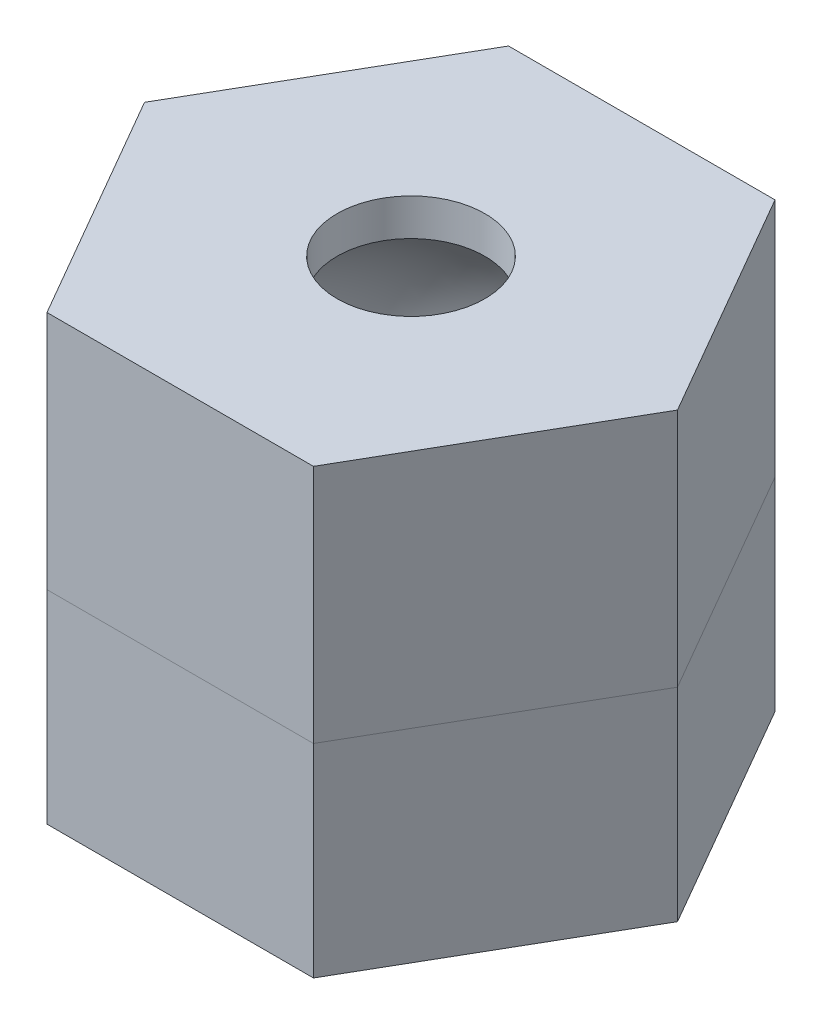
SolidWorks part; units mm, degrees
other "Downer"
other "Upper"
material "ABS"
ref_plane "Front Plane" through (0, 0, 0) normal (0, 0, 1) x (1, 0, 0)
ref_plane "Top Plane" through (0, 0, 0) normal (0, 1, 0) x (1, 0, 0)
ref_plane "Right Plane" through (0, 0, 0) normal (1, 0, 0) x (0, 0, -1)
sketch "Sketch2" plane through (0, 0, 0) normal (0, 1, 0) x (1, 0, 0)
  line L1 (72.1688, 0) -> (36.0844, 62.5)
  line L2 (36.0844, 62.5) -> (-36.0844, 62.5)
  line L3 (-36.0844, 62.5) -> (-72.1688, 0)
  line L4 (-72.1688, 0) -> (-36.0844, -62.5)
  line L5 (-36.0844, -62.5) -> (36.0844, -62.5)
  line L6 (36.0844, -62.5) -> (72.1688, 0)
  circle A0 centre (0, 0) radius 62.5 construction
  dimension "D1" = 125
extrude "Boss" add sketch "Sketch2" along normal blind 110
sketch "Sketch3" plane through (0, 0, 0) normal (1, 0, 0) x (0, 0, -1)
  line L0 (0, 110) -> (0, 7.5305)
  line L1 (0, 110) -> (0, 0) construction
  line L2 (0, 110) -> (20, 110)
  line L3 (0, 7.5305) -> (20, 7.5305)
  arc A0 (20, 7.5305) -> (20, 110) centre (0, 58.7652) ccw
  dimension "D2" = 110
  dimension "D1" = 20
revolve "Void" cut sketch "Sketch3" angle 360 about L0
ref_plane "Split Plane" through (0, 55, 0) normal (0, 1, 0) x (1, 0, 0)
split "Split" trim tools "Split Plane" bodies to split 102 resulting bodies 104 105
sketch "Sketch6" plane through (0, 55, 0) normal (0, 1, 0) x (1, 0, 0)
  circle A0 centre (62.5, 0) radius 5
  circle A1 centre (31.25, -54.1266) radius 5
  circle A2 centre (-31.25, -54.1266) radius 5
  circle A3 centre (-62.5, 0) radius 5
  circle A4 centre (-31.25, 54.1266) radius 5
  circle A5 centre (31.25, 54.1266) radius 5
  point P2 (34.8698, -68.7666)
  point P3 (0, 0)
  point P4 (-29.077, -55.3243)
  point P16 (0, 0)
  point P17 (0, 0)
  dimension "D2" = 10
  dimension "D1" = 62.5
  dimension "D3" = 6
extrude "Tab Holes" cut sketch "Sketch6" along direction (0, 1, 0) on the side of the normal blind 11
sketch "Sketch7" plane through (0, 55, 0) normal (0, 1, 0) x (1, 0, 0)
  circle A6 centre (62.5, 0) radius 5 construction
  circle A7 centre (62.5, 0) radius 5 construction
  circle A8 centre (62.5, 0) radius 4.5
  circle A9 centre (31.25, -54.1266) radius 4.5
  circle A10 centre (-31.25, -54.1266) radius 4.5
  circle A11 centre (-62.5, 0) radius 4.5
  circle A18 centre (-31.25, 54.1266) radius 4.5
  circle A19 centre (31.25, 54.1266) radius 4.5
  point P6 (29.1748, 48.4165)
  point P7 (0, 0)
  point P17 (0, 0)
  dimension "D1" = 9
extrude "Tabs" add sketch "Sketch7" along normal blind 10
sketch "Sketch8" plane through (0, 110, 0) normal (0, 1, 0) x (1, 0, 0)
  line L0 (36.0844, -62.5) -> (72.1688, 0)
  line L8 (36.0844, -62.5) -> (72.1688, 0)
  line L9 (-36.0844, -62.5) -> (36.0844, -62.5)
  line L10 (-36.0844, -62.5) -> (36.0844, -62.5)
  line L11 (-72.1688, 0) -> (-36.0844, -62.5)
  line L12 (-72.1688, 0) -> (-36.0844, -62.5)
  line L13 (-36.0844, 62.5) -> (-72.1688, 0)
  line L14 (-36.0844, 62.5) -> (-72.1688, 0)
  line L15 (36.0844, 62.5) -> (-36.0844, 62.5)
  line L16 (36.0844, 62.5) -> (-36.0844, 62.5)
  line L17 (72.1688, 0) -> (36.0844, 62.5)
  line L18 (72.1688, 0) -> (36.0844, 62.5)
  circle A2 centre (0, 0) radius 20 construction
  circle A3 centre (0, 0) radius 20
extrude "Spout" add sketch "Sketch8" along normal blind 10
ref_plane "Spout Plane" through (0, 110, 0) normal (0, -1, 0) x (-1, 0, 0)
ref_plane "Mid Plane" through (0, 58.7652, 0) normal (0, -1, 0) x (-1, 0, 0)
